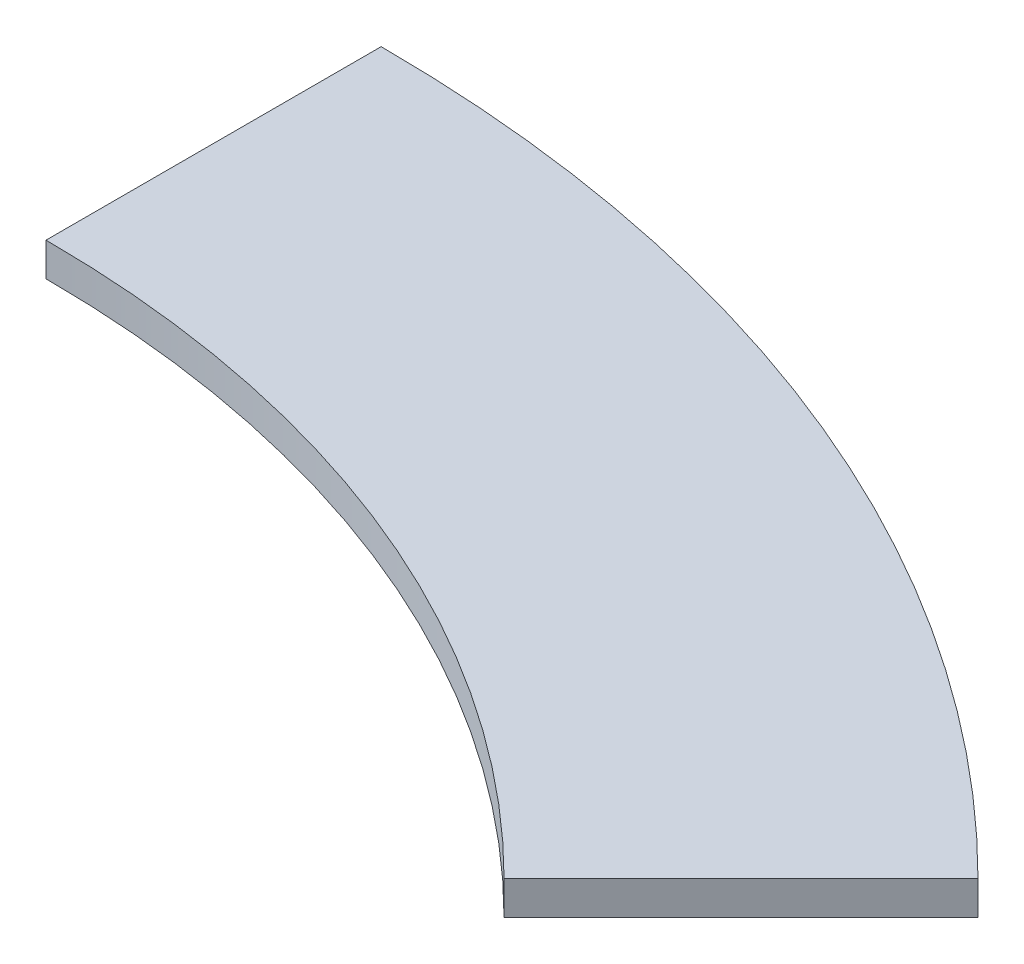
SolidWorks part; units mm, degrees
ref_plane "Front Plane" through (0, 0, 0) normal (0, 0, 1) x (1, 0, 0)
ref_plane "Top Plane" through (0, 0, 0) normal (0, 1, 0) x (1, 0, 0)
ref_plane "Right Plane" through (0, 0, 0) normal (1, 0, 0) x (0, 0, -1)
sketch "Sketch1" plane through (0, 0, 0) normal (0, 1, 0) x (1, 0, 0)
  line L0 (0, 0) -> (0, 330) construction
  line L1 (0, 330) -> (0, 430)
  line L2 (0, 0) -> (304.0559, 304.0559) construction
  line L3 (233.3452, 233.3452) -> (304.0559, 304.0559)
  arc A0 (0, 330) -> (233.3452, 233.3452) centre (0, 0) cw
  arc A1 (0, 430) -> (304.0559, 304.0559) centre (0, 0) cw
  dimension "D1" = 330
  dimension "D2" = 100
  dimension "D3" = 430
  dimension "D4" = 45
extrude "Boss-Extrude1" add sketch "Sketch1" along normal blind 10 contours A1 L1 A0 L3
